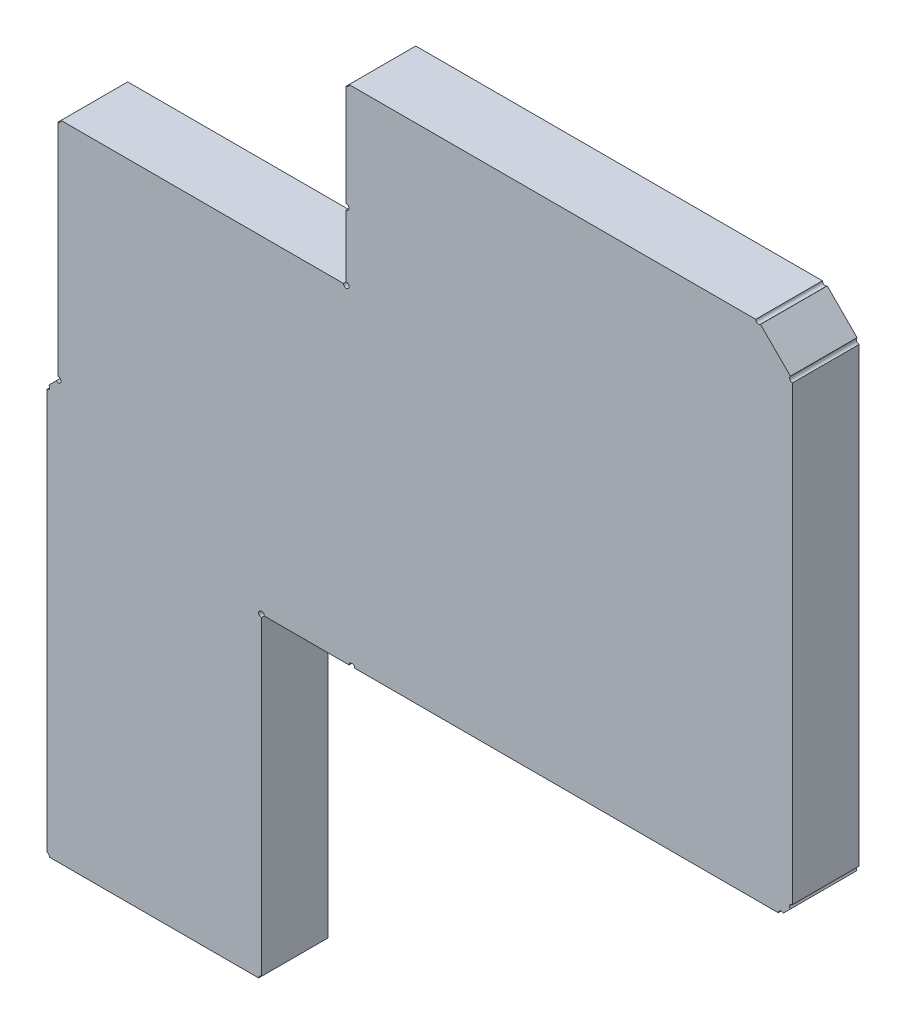
SolidWorks part; units mm, degrees
ref_plane "前视基准面" through (0, 0, 0) normal (0, 0, 1) x (1, 0, 0)
ref_plane "上视基准面" through (0, 0, 0) normal (0, 1, 0) x (1, 0, 0)
ref_plane "右视基准面" through (0, 0, 0) normal (1, 0, 0) x (0, 0, -1)
sketch "草图1" plane through (0, 0, 0) normal (0, 0, 1) x (1, 0, 0)
  line L0 (90.932, 85.09) -> (91.186, 85.344)
  line L1 (90.932, 75.946) -> (90.932, 85.09)
  line L2 (90.932, 75.946) -> (95.758, 75.946)
  line L3 (95.758, 75.946) -> (95.758, 83.058)
  line L4 (95.758, 83.058) -> (97.79, 83.058)
  line L5 (97.79, 83.058) -> (107.442, 83.058)
  line L6 (107.442, 83.058) -> (107.696, 83.312)
  line L7 (107.696, 83.312) -> (107.696, 93.599)
  line L8 (106.934, 94.361) -> (107.696, 93.599)
  line L9 (97.663, 94.361) -> (106.934, 94.361)
  line L10 (97.663, 91.948) -> (97.663, 94.361)
  line L11 (97.663, 90.424) -> (97.663, 91.948)
  line L12 (91.186, 90.424) -> (97.663, 90.424)
  line L13 (91.186, 85.344) -> (91.186, 90.424)
  circle A0 centre (90.932, 85.09) radius 0.0635
  circle A1 centre (91.186, 85.344) radius 0.0635
  circle A2 centre (90.932, 75.946) radius 0.0635
  circle A3 centre (90.932, 85.09) radius 0.0635
  circle A4 centre (90.932, 75.946) radius 0.0635
  circle A5 centre (95.758, 75.946) radius 0.0635
  circle A6 centre (95.758, 75.946) radius 0.0635
  circle A7 centre (95.758, 83.058) radius 0.0635
  circle A8 centre (95.758, 83.058) radius 0.0635
  circle A9 centre (97.79, 83.058) radius 0.0635
  circle A10 centre (97.79, 83.058) radius 0.0635
  circle A11 centre (107.442, 83.058) radius 0.0635
  circle A12 centre (107.442, 83.058) radius 0.0635
  circle A13 centre (107.696, 83.312) radius 0.0635
  circle A14 centre (107.696, 83.312) radius 0.0635
  circle A15 centre (107.696, 93.599) radius 0.0635
  circle A16 centre (106.934, 94.361) radius 0.0635
  circle A17 centre (107.696, 93.599) radius 0.0635
  circle A18 centre (97.663, 94.361) radius 0.0635
  circle A19 centre (106.934, 94.361) radius 0.0635
  circle A20 centre (97.663, 91.948) radius 0.0635
  circle A21 centre (97.663, 94.361) radius 0.0635
  circle A22 centre (97.663, 90.424) radius 0.0635
  circle A23 centre (97.663, 91.948) radius 0.0635
  circle A24 centre (91.186, 90.424) radius 0.0635
  circle A25 centre (97.663, 90.424) radius 0.0635
  circle A26 centre (91.186, 85.344) radius 0.0635
  circle A27 centre (91.186, 90.424) radius 0.0635
extrude "凸台-拉伸1" add sketch "草图1" along normal blind 1.5 contours A24 L13 A1 L0 A0 L1 A2 L2 A5 L3 A7 L4 A9 L5 A11 L6 A13 L7 A15 L8 A16 L9 A18 L10 A20 L11 A22 L12
